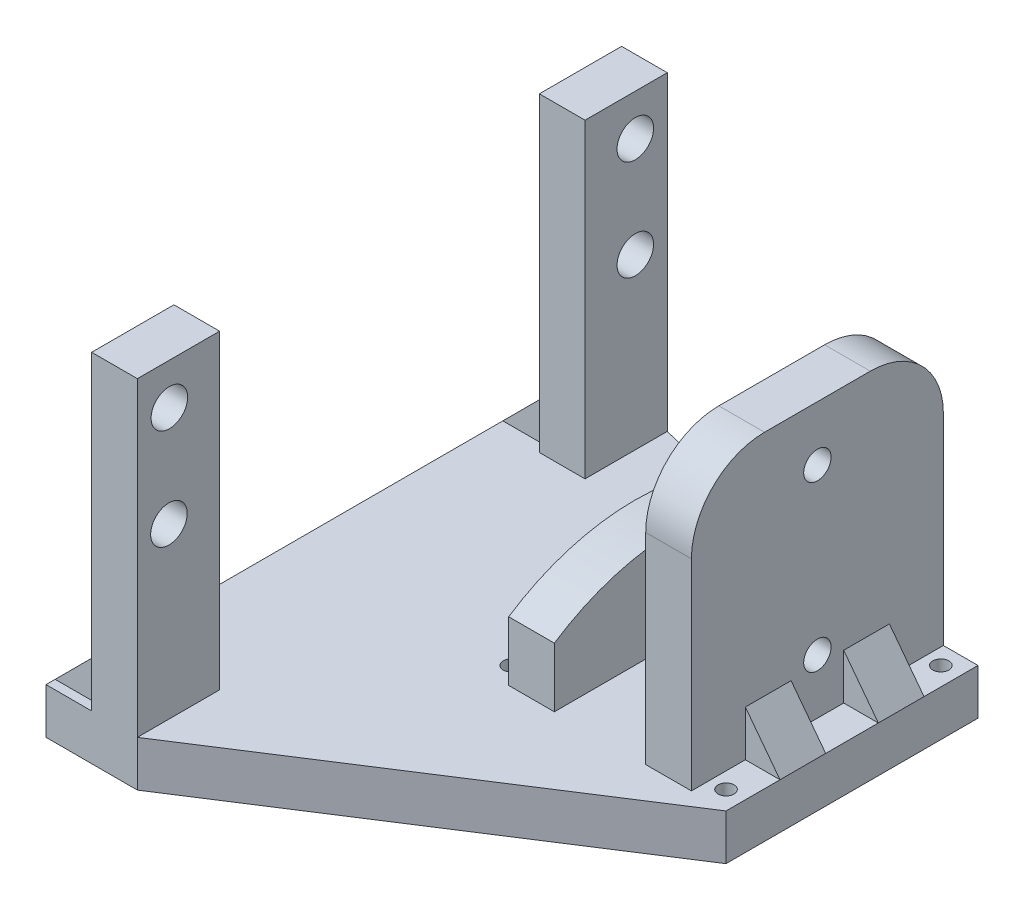
SolidWorks part; units mm, degrees
ref_plane "Front Plane" through (0, 0, 0) normal (0, 0, 1) x (1, 0, 0)
ref_plane "Top Plane" through (0, 0, 0) normal (0, 1, 0) x (1, 0, 0)
ref_plane "Right Plane" through (0, 0, 0) normal (1, 0, 0) x (0, 0, -1)
sketch "Sketch1" plane through (0, 0, 0) normal (0, 1, 0) x (1, 0, 0)
  line L0 (0, 13.7892) -> (27.5784, 13.7892) construction
  line L5 (0, 0) -> (27.5784, 0)
  line L6 (0, 0) -> (0, 27.5784)
  line L7 (0, 27.5784) -> (27.5784, 27.5784)
  line L8 (27.5784, 0) -> (27.5784, 27.5784)
  line L9 (13.7892, 0) -> (13.7892, 27.5784) construction
  line L10 (13.7892, 13.7892) -> (27.5784, 27.5784) construction
  line L11 (26.1642, 26.1642) -> (27.5784, 27.5784)
  line L12 (13.7892, 13.7892) -> (0, 27.5784) construction
  line L13 (1.4142, 26.1642) -> (0, 27.5784)
  line L14 (13.7892, 13.7892) -> (0, 0) construction
  line L15 (1.4142, 1.4142) -> (0, 0)
  line L16 (13.7892, 13.7892) -> (27.5784, 0) construction
  line L17 (26.1608, 1.4108) -> (27.5784, 0)
  circle A6 centre (2.0329, 2.0329) radius 0.875
  circle A8 centre (25.5455, 25.5455) radius 0.875
  circle A9 centre (2.0329, 25.5455) radius 0.875
  circle A10 centre (25.5455, 2.0329) radius 0.875
  dimension "D7" = 2
  dimension "D8" = 2
  dimension "D9" = 2
  dimension "D10" = 45
  dimension "D3" = 2
  dimension "D4" = 1.75
  dimension "D5" = 1.75
  dimension "D6" = 1.75
  dimension "D2" = 1.75
  dimension "D1" = 19.5009
  dimension "D11" = 45
  dimension "D12" = 45
extrude "Boss-Extrude1" add sketch "Sketch1" along normal blind 5
sketch "Sketch2" plane through (0, 5, 0) normal (0, 1, 0) x (1, 0, 0)
  line L0 (0, 13.7892) -> (27.5784, 13.7892) construction
  line L1 (0, 0) -> (0, 27.5784) construction
  line L2 (27.5784, 0) -> (27.5784, 27.5784) construction
  line L3 (13.7892, 27.5784) -> (13.7892, 0) construction
  line L4 (0, 27.5784) -> (27.5784, 27.5784) construction
  line L5 (0, 0) -> (27.5784, 0) construction
  line L7 (18.7892, 27.5784) -> (18.7892, 0)
  line L10 (8.7892, 0) -> (8.7892, 27.5784)
  line L12 (3.7892, 27.5784) -> (3.7892, 0)
  line L13 (3.7892, 0) -> (8.7892, 0)
  line L14 (3.7892, 27.5784) -> (8.7892, 27.5784)
  line L15 (18.7892, 27.5784) -> (23.7892, 27.5784)
  line L16 (23.7892, 27.5784) -> (23.7892, 0)
  line L17 (23.7892, 0) -> (18.7892, 0)
  dimension "D1" = 5
  dimension "D2" = 5
  dimension "D3" = 5
  dimension "D4" = 5
extrude "Boss-Extrude2" add sketch "Sketch2" along normal blind 30
sketch "Sketch3" plane through (23.7892, 0, 0) normal (1, 0, 0) x (0, 0, -1)
sketch "Sketch4" plane through (3.7892, 0, 0) normal (-1, 0, 0) x (0, 0, 1)
  line L0 (-13.7892, 35) -> (-13.7892, 0) construction
  line L1 (-27.5784, 35) -> (0, 35) construction
  line L2 (0, 0) -> (-27.5784, 0) construction
  line L3 (-27.5784, 11.5094) -> (-27.5784, 35)
  line L4 (-27.5784, 35) -> (-27.5784, 5) construction
  line L5 (-27.5784, 35) -> (0, 35)
  line L6 (0, 35) -> (0, 11.5094)
  line L7 (0, 35) -> (0, 5) construction
  arc A0 (0, 11.5094) -> (-27.5784, 11.5094) centre (-13.7892, -9.3439) ccw
  dimension "D1" = 50
extrude "Cut-Extrude2" cut sketch "Sketch4" against normal blind 10
sketch "Sketch5" plane through (23.7892, 0, 0) normal (1, 0, 0) x (0, 0, -1)
  line L0 (13.7892, 35) -> (13.7892, 5) construction
  line L1 (0, 35) -> (27.5784, 35) construction
  line L2 (0, 5) -> (27.5784, 5) construction
  line L3 (27.5784, 20) -> (0, 20) construction
  line L4 (27.5784, 35) -> (27.5784, 5) construction
  line L5 (0, 35) -> (0, 5) construction
  line L6 (13.7892, 27.5) -> (13.7892, 12.5)
  line L7 (13.7892, 20) -> (13.7892, 12.5) construction
  circle A0 centre (13.7892, 29) radius 1.5
  circle A1 centre (13.7892, 11) radius 1.5
  dimension "D1" = 3
  dimension "D2" = 3
  dimension "D3" = 15
  dimension "D4" = 7.5
extrude "Cut-Extrude3" cut sketch "Sketch5" against normal blind 24 contours A0 | A1
fillet "Fillet1" radius 8 1 edges at (21.2892, 35, 0)
fillet "Fillet2" radius 8 1 edges at (21.2892, 35, -27.5784)
sketch "Sketch6" plane through (0, 5, 0) normal (0, 1, 0) x (1, 0, 0)
  line L5 (0, 13.7892) -> (27.5784, 13.7892) construction
  line L6 (0, 0) -> (0, 27.5784) construction
  line L7 (27.5784, 0) -> (27.5784, 27.5784) construction
  line L8 (18.7892, 27.5784) -> (18.7892, 0) construction
  line L9 (8.7892, 27.5784) -> (18.7892, 27.5784)
  line L10 (8.7892, 27.5784) -> (8.7892, 17.5784)
  line L11 (8.7892, 17.5784) -> (18.7892, 17.5784)
  line L12 (18.7892, 27.5784) -> (18.7892, 17.5784)
  dimension "D2" = 10
extrude "Cut-Extrude5" cut sketch "Sketch6" against normal blind 7
sketch "Sketch7" plane through (0, 0, 0) normal (0, -1, 0) x (1, 0, 0)
  line L0 (0, -13.7892) -> (27.5784, -13.7892) construction
  line L1 (0, 0) -> (0, -27.5784) construction
  line L2 (27.5784, 0) -> (27.5784, -27.5784) construction
  line L3 (13.7892, 0) -> (13.7892, -17.5784) construction
  line L4 (0, 0) -> (27.5784, 0) construction
  line L5 (8.7892, -17.5784) -> (18.7892, -17.5784) construction
  circle A0 centre (13.7892, -13.7892) radius 3
  dimension "D1" = 6
extrude "Cut-Extrude6" cut sketch "Sketch7" against normal blind 7 contours A0
sketch "Sketch8" plane through (0, 5, 0) normal (0, 1, 0) x (1, 0, 0)
  line L0 (27.5784, 0) -> (27.5784, 27.5784) construction
  line L1 (27.5784, 21.6705) -> (23.7892, 21.6705)
  line L2 (27.5784, 21.6705) -> (27.5784, 22.5392)
  line L4 (23.7892, 21.6705) -> (23.7892, 22.5392)
  line L5 (23.7892, 0) -> (23.7892, 27.5784) construction
  line L6 (25.5455, 2.9079) -> (25.5455, 5.9079) construction
  line L7 (27.5784, 5.9079) -> (23.7892, 5.9079)
  line L8 (27.5784, 5.9079) -> (27.5784, 10.9079)
  line L9 (27.5784, 10.9079) -> (23.7892, 10.9079)
  line L10 (23.7892, 5.9079) -> (23.7892, 10.9079)
  line L11 (25.5455, 24.6705) -> (25.5455, 21.6705) construction
  line L12 (3.7892, 27.5784) -> (3.7892, 0) construction
  line L13 (23.7892, 21.6705) -> (27.5784, 21.6705)
  line L14 (23.7892, 21.6705) -> (23.7892, 16.6705)
  line L15 (23.7892, 16.6705) -> (27.5784, 16.6705)
  line L16 (27.5784, 21.6705) -> (27.5784, 16.6705)
  line L21 (0, 0) -> (0, 27.5784) construction
  line L22 (23.7892, 16.6705) -> (0, 16.6705) construction
  line L23 (3.7892, 10.9079) -> (0, 10.9079)
  line L24 (3.7892, 10.9079) -> (3.7892, 5.9079)
  line L25 (3.7892, 5.9079) -> (0, 5.9079)
  line L26 (0, 10.9079) -> (0, 5.9079)
  line L27 (23.7892, 21.6705) -> (0, 21.6705) construction
  line L28 (23.7892, 10.9079) -> (0, 10.9079) construction
  line L29 (23.7892, 5.9079) -> (0, 5.9079) construction
  line L30 (3.7892, 27.5784) -> (3.7892, 0) construction
  line L31 (0, 21.6705) -> (3.7892, 21.6705)
  line L32 (0, 21.6705) -> (0, 16.6705)
  line L33 (0, 16.6705) -> (3.7892, 16.6705)
  line L34 (3.7892, 21.6705) -> (3.7892, 16.6705)
  circle A0 centre (25.5455, 2.0329) radius 0.875 construction
  circle A1 centre (25.5455, 25.5455) radius 0.875 construction
  line M11 (23.7892, 27.5784) -> (23.7892, 0)
  line M13 (27.5784, 0) -> (27.5784, 27.5784)
  dimension "D1" = 3
  dimension "D2" = 3
  dimension "D3" = 5
  dimension "D4" = 5
extrude "Boss-Extrude3" add sketch "Sketch8" along normal blind 5 contours L34 L31 L32 L33 | L15 L1 M11 M13 | L9 L7 M13 M11 | L23 L26 L25 L24
sketch "Sketch9" plane through (0, 0, -5.9079) normal (0, 0, 1) x (1, 0, 0)
  line L0 (0, 5) -> (3.7892, 10)
  line L1 (3.7892, 10) -> (0, 10)
  line L2 (0, 10) -> (0, 5)
  line L3 (23.7892, 10) -> (27.5784, 5)
  line L4 (27.5784, 5) -> (27.5784, 10)
  line L5 (27.5784, 10) -> (23.7892, 10)
extrude "Cut-Extrude7" cut sketch "Sketch9" against normal blind 25 contours L2 L0 L1 | L5 L3 L4
sketch "Sketch10" plane through (0, 0, 0) normal (-1, 0, 0) x (0, 0, 1)
  line L1 (-27.5784, 5) -> (0, 5)
  line L2 (-27.5784, 5) -> (-27.5784, 0)
  line L3 (-27.5784, 0) -> (0, 0)
  line L4 (0, 5) -> (0, 0)
extrude "Boss-Extrude4" add sketch "Sketch10" along normal blind 11.61
sketch "Sketch11" plane through (-11.61, 0, 0) normal (-1, 0, 0) x (0, 0, 1)
  line L3 (-32.7584, 9.0171) -> (-32.7584, 0)
  line L4 (-32.7584, 0) -> (-27.5784, 0)
  line L6 (0, 0) -> (25.24, 0)
  line L8 (-32.7584, 9.0171) -> (-32.7584, 39)
  line L9 (-32.7584, 39) -> (-23.7584, 39)
  line L10 (-23.7584, 5) -> (-23.7584, 39)
  line L11 (25.24, 0) -> (25.24, 9.0171)
  line L12 (16.24, 5) -> (0, 5)
  line L14 (-27.5784, 0) -> (0, 0)
  line L16 (25.24, 9.0171) -> (25.24, 39)
  line L17 (25.24, 39) -> (16.24, 39)
  line L18 (16.24, 5) -> (16.24, 39)
  line L19 (0, 5) -> (-23.7584, 5)
  dimension "D1" = 39.9984
  dimension "D2" = 9
  dimension "D3" = 34
  dimension "D4" = 9
  dimension "D5" = 34
extrude "Boss-Extrude5" add sketch "Sketch11" along normal blind 5
sketch "Sketch17" plane through (-16.61, 0, 0) normal (-1, 0, 0) x (0, 0, 1)
  line L0 (-23.7584, 5) -> (-32.7584, 5)
  line L1 (-32.7584, 39) -> (-32.7584, 0) construction
  line L2 (-32.7584, 5) -> (-32.7584, 0)
  line L3 (-32.7584, 0) -> (25.24, 0)
  line L4 (25.24, 0) -> (25.24, 5)
  line L5 (25.24, 0) -> (25.24, 39) construction
  line L6 (25.24, 5) -> (-23.7584, 5)
extrude "Boss-Extrude9" add sketch "Sketch17" along normal blind 5
sketch "Sketch18" plane through (0, 5, 0) normal (0, 1, 0) x (1, 0, 0)
  line L0 (-16.61, 23.7584) -> (-16.61, 32.7584) construction
  line L1 (-16.61, 31.7584) -> (-21.61, 31.7584)
  line L2 (-16.61, 31.7584) -> (-16.61, 24.7584)
  line L3 (-16.61, 24.7584) -> (-21.61, 24.7584)
  line L4 (-21.61, 31.7584) -> (-21.61, 24.7584)
  line L5 (-21.61, -25.24) -> (-21.61, 32.7584) construction
  line L6 (-16.61, -25.24) -> (-16.61, -16.24) construction
  line L7 (-21.61, -17.24) -> (-16.61, -17.24)
  line L8 (-21.61, -17.24) -> (-21.61, -24.24)
  line L9 (-21.61, -24.24) -> (-16.61, -24.24)
  line L10 (-16.61, -17.24) -> (-16.61, -24.24)
  line L11 (-21.61, 32.7584) -> (-16.61, 32.7584) construction
  line L12 (-16.61, 23.7584) -> (-11.61, 23.7584) construction
  line L13 (-16.61, -16.24) -> (-11.61, -16.24) construction
  line L14 (-16.61, -25.24) -> (-11.61, -25.24) construction
  dimension "D1" = 1
  dimension "D2" = 1
  dimension "D3" = 1
  dimension "D4" = 1
extrude "Boss-Extrude10" add sketch "Sketch18" along normal blind 5
sketch "Sketch19" plane through (0, 0, 24.24) normal (0, 0, 1) x (1, 0, 0)
  line L0 (-21.61, 5) -> (-21.61, 10)
  line L1 (-21.61, 10) -> (-16.61, 10)
  line L2 (-16.61, 10) -> (-21.61, 5)
extrude "Cut-Extrude9" cut sketch "Sketch19" against normal blind 59
sketch "Sketch20" plane through (-11.61, 0, 0) normal (1, 0, 0) x (0, 0, -1)
  circle A0 centre (-21.7387, 34.5013) radius 2
  circle A1 centre (-21.7853, 23.5013) radius 2
  circle A2 centre (29.2608, 23.4989) radius 2
  circle A3 centre (29.2613, 34.4989) radius 2
extrude "Cut-Extrude10" cut sketch "Sketch20" against normal blind 10 contours A0 | A1 | A3 | A2
sketch "Sketch21" plane through (0, 5, 0) normal (0, 1, 0) x (1, 0, 0)
  line L0 (-11.61, -25.24) -> (27.5784, 0)
  line L1 (27.5784, 0) -> (-11.61, 0)
  line L2 (-11.61, 0) -> (-11.61, -25.24)
  line L3 (-11.61, 32.7584) -> (8.7892, 27.5784)
  line L4 (8.7892, 27.5784) -> (-11.61, 27.5784)
  line L5 (-11.61, 27.5784) -> (-11.61, 32.7584)
extrude "Boss-Extrude11" add sketch "Sketch21" against normal blind 5
